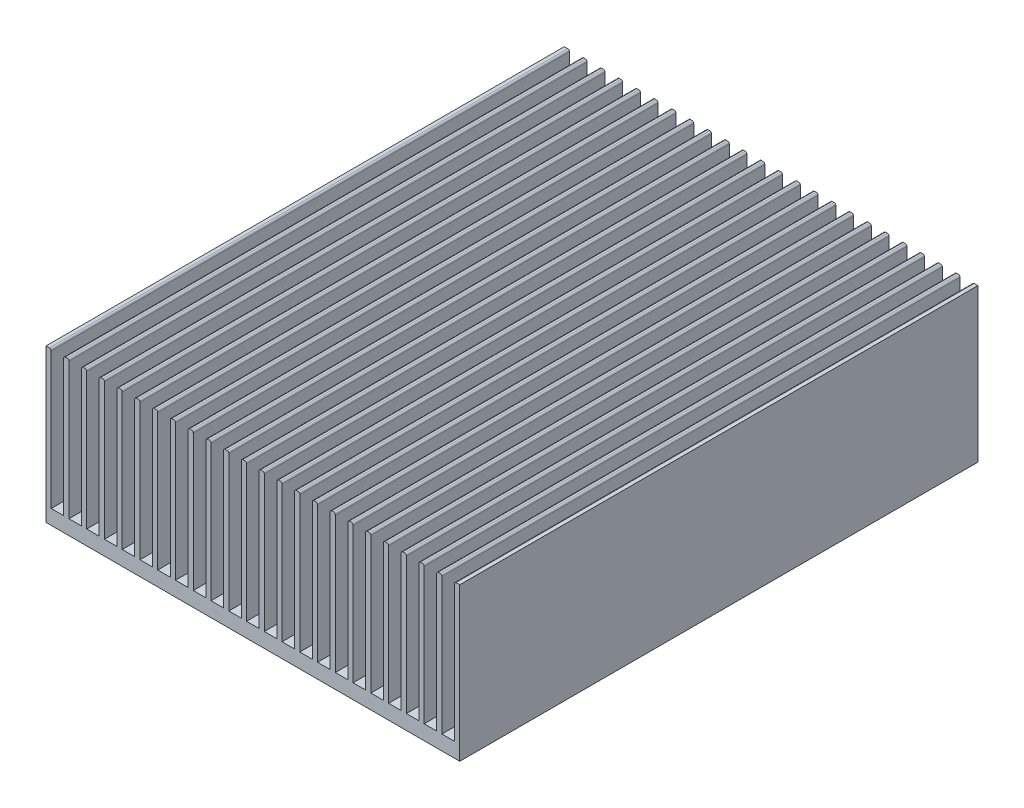
SolidWorks part; units mm, degrees
ref_plane "Front" through (0, 0, 0) normal (0, 0, 1) x (1, 0, 0)
ref_plane "Top" through (0, 0, 0) normal (0, 1, 0) x (1, 0, 0)
ref_plane "Right" through (0, 0, 0) normal (1, 0, 0) x (0, 0, -1)
sketch "Sketch1" plane through (0, 0, 0) normal (0, 0, 1) x (1, 0, 0)
  line L1 (0, 0) -> (121.666, 0)
  line L2 (0, 0) -> (0, 44.958)
  line L3 (0, 44.958) -> (121.666, 44.958)
  line L4 (121.666, 0) -> (121.666, 44.958)
  dimension "D1" = 44.958
  dimension "D2" = 121.666
extrude "Extrude1" add sketch "Sketch1" against normal blind 152.4
sketch "Sketch2" plane through (0, 0, 0) normal (0, 0, 1) x (1, 0, 0)
  line L0 (0, 0) -> (121.666, 0) construction
  line L1 (1.524, 47.6109) -> (5.207, 47.6109)
  line L2 (1.524, 47.6109) -> (1.524, 4.318)
  line L3 (1.524, 4.318) -> (5.207, 4.318)
  line L4 (5.207, 47.6109) -> (5.207, 4.318)
  line L5 (0, 44.958) -> (0, 0) construction
  dimension "D1" = 4.318
  dimension "D2" = 1.524
  dimension "D3" = 3.683
extrude "Extrude2" cut sketch "Sketch2" against normal blind 152.4
fillet "Fillet1" radius 0.508 2 edges at (5.207, 44.958, -76.2) (1.524, 44.958, -76.2)
pattern_linear "LPattern1" count 23 spacing 5.2222 along (1, 0, 0) of "Fillet1", "Extrude2"
sketch "Sketch4" plane through (0, 0, 0) normal (0, -1, 0) x (1, 0, 0)
  line L0 (0, -152.4) -> (0, 0) construction
  circle A0 centre (34.671, -43.18) radius 1.5875
  circle A1 centre (88.011, -109.22) radius 1.5875
  dimension "D1" = 3.175
  dimension "D2" = 3.175
  dimension "D3" = 34.671
  dimension "D4" = 66.04
  dimension "D6" = 53.34
extrude "Extrude3" cut sketch "Sketch4" against normal blind 3.81
sketch "Sketch5" plane through (0, 0, 0) normal (0, -1, 0) x (1, 0, 0)
  line L0 (0, -152.4) -> (0, 0) construction
  line L1 (0, -152.4) -> (121.666, -152.4) construction
  circle A0 centre (25.908, -43.18) radius 1.5875
  circle A1 centre (95.758, -109.22) radius 1.5875
  dimension "D3" = 3.175
  dimension "D4" = 3.175
  dimension "D1" = 43.18
  dimension "D2" = 109.22
  dimension "D5" = 25.908
  dimension "D6" = 69.85
extrude "Extrude4" cut sketch "Sketch5" against normal blind 3.81
sketch "Sketch6" plane through (0, 0, 0) normal (0, -1, 0) x (1, 0, 0)
  line L4 (95.5243, 0) -> (99.2073, 0) construction
  circle A0 centre (25.908, -13.081) radius 1.778
  circle A1 centre (95.758, -13.081) radius 1.778
  circle A2 centre (25.908, -63.9318) radius 1.778
  circle A3 centre (95.758, -63.9318) radius 1.778
  circle A4 centre (25.908, -140.081) radius 1.778
  circle A5 centre (95.758, -140.081) radius 1.778
  point P17 (97.3658, 0)
  dimension "D1" = 3.556
  dimension "D2" = 3.556
  dimension "D3" = 3.556
  dimension "D4" = 3.556
  dimension "D5" = 3.556
  dimension "D6" = 3.556
  dimension "D8" = 69.85
  dimension "D10" = 69.85
  dimension "D12" = 69.85
  dimension "D13" = 127
  dimension "D14" = 127
  dimension "D15" = 76.1492
  dimension "D16" = 76.1492
  dimension "D17" = 13.081
  dimension "D18" = 13.081
extrude "Extrude5" cut sketch "Sketch6" against normal blind 3.81
